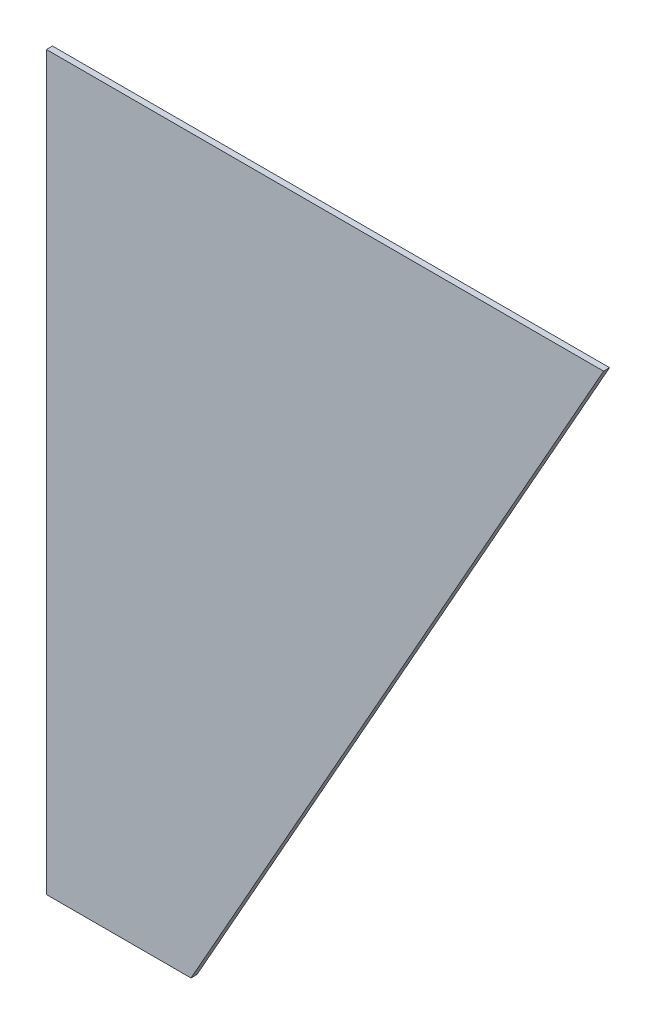
SolidWorks part; units mm, degrees
material "Acrílico (médio-alto impacto)"
ref_plane "Plano frontal" through (0, 0, 0) normal (0, 0, 1) x (1, 0, 0)
ref_plane "Plano superior" through (0, 0, 0) normal (0, 1, 0) x (1, 0, 0)
ref_plane "Plano direito" through (0, 0, 0) normal (1, 0, 0) x (0, 0, -1)
sketch "Esboço1" plane through (0, 0, 0) normal (0, 0, 1) x (1, 0, 0)
  line L0 (0, 0) -> (185, 0)
  line L1 (0, 0) -> (0, -243)
  line L2 (0, -243) -> (48, -243)
  line L3 (48, -243) -> (185, 0)
  dimension "D1" = 243
  dimension "D2" = 48
  dimension "D3" = 185
extrude "Ressalto-extrusão1" add sketch "Esboço1" along normal blind 2
